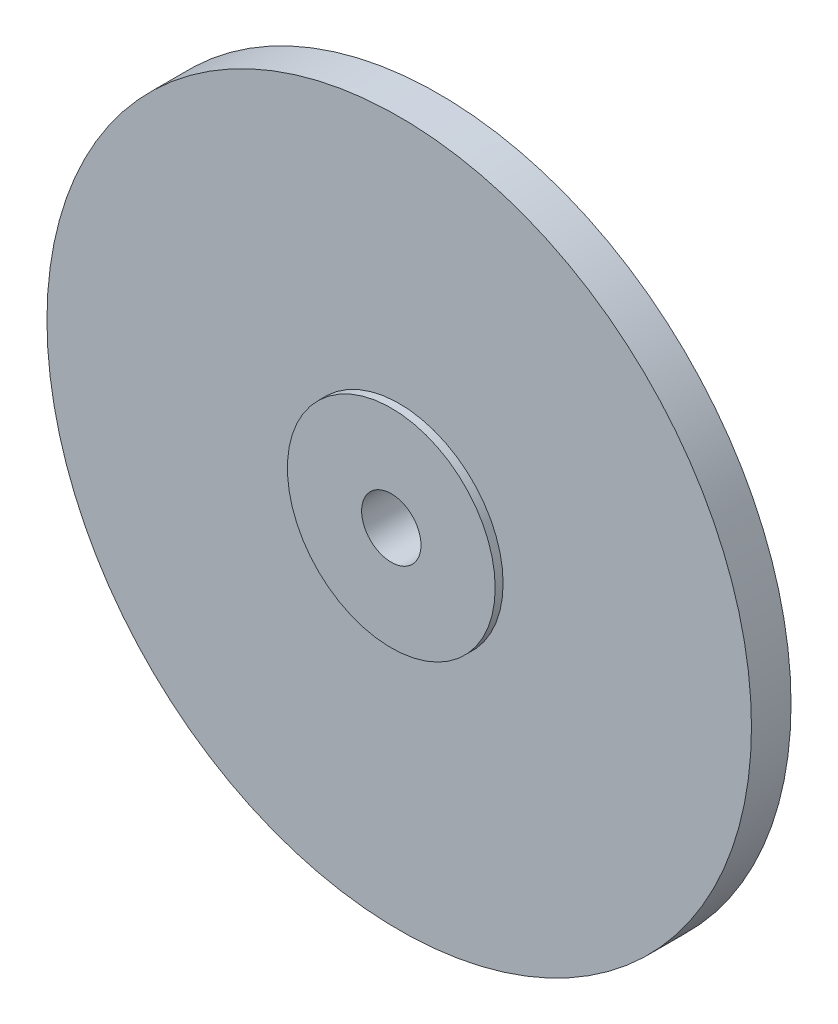
SolidWorks part; units mm, degrees
ref_plane "正面" through (0, 0, 0) normal (0, 0, 1) x (1, 0, 0)
ref_plane "平面" through (0, 0, 0) normal (0, 1, 0) x (1, 0, 0)
ref_plane "右側面" through (0, 0, 0) normal (1, 0, 0) x (0, 0, -1)
sketch "ｽｹｯﾁ1" plane through (0, 0, 0) normal (0, 0, 1) x (1, 0, 0)
  circle A0 centre (0, 0) radius 17.8
  point P3 (0, 0)
extrude "ﾎﾞｽ - 押し出し1" add sketch "ｽｹｯﾁ1" along normal blind 2
sketch "ｽｹｯﾁ2" plane through (0, 0, 0) normal (0, 0, -1) x (-1, 0, 0)
  circle A0 centre (0, 0) radius 7.85
extrude "ﾎﾞｽ - 押し出し2" add sketch "ｽｹｯﾁ2" along normal blind 0.8
draft "抜き勾配1" type of draft neutral plane draft angle 1 faces to draft 1 face at (-7.85, 0, -0.8) neutral plane through (0, 0, -0.8) neutral plane normal (0, 0, -1) parameters "D1"=1
sketch "ｽｹｯﾁ38" plane through (0, 0, -0.8) normal (0, 0, -1) x (-1, 0, 0)
  circle A0 centre (0, 0) radius 4.8
extrude "ﾎﾞｽ - 押し出し3" add sketch "ｽｹｯﾁ38" along normal blind 1.9
sketch "ｽｹｯﾁ39" plane through (0, 0, 2) normal (0, 0, 1) x (1, 0, 0)
  circle A0 centre (0, 0) radius 5.25
extrude "ﾎﾞｽ - 押し出し4" add sketch "ｽｹｯﾁ39" along normal blind 0.4
sketch "ｽｹｯﾁ40" plane through (0, 0, 2.4) normal (0, 0, 1) x (1, 0, 0)
  circle A0 centre (0, 0) radius 1.5
extrude "ｶｯﾄ - 押し出し1" cut sketch "ｽｹｯﾁ40" against normal blind 10.4
